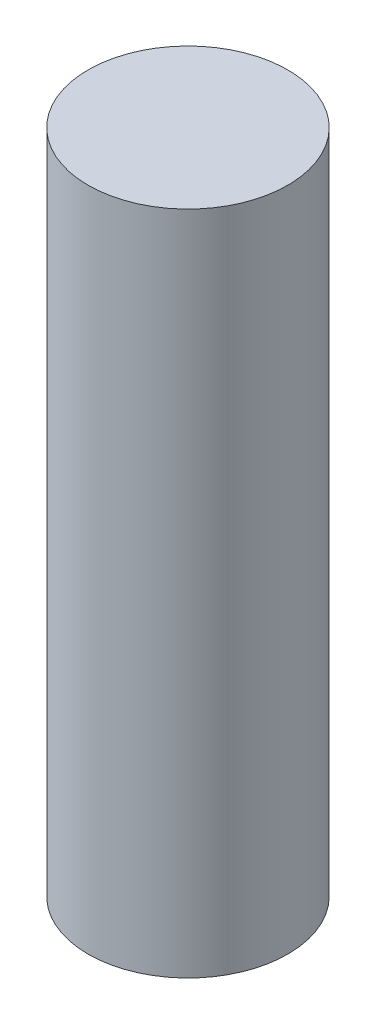
SolidWorks part; units mm, degrees
ref_plane "Front Plane" through (0, 0, 0) normal (0, 0, 1) x (1, 0, 0)
ref_plane "Top Plane" through (0, 0, 0) normal (0, 1, 0) x (1, 0, 0)
ref_plane "Right Plane" through (0, 0, 0) normal (1, 0, 0) x (0, 0, -1)
sketch "Sketch1" plane through (0, 0, 0) normal (0, 1, 0) x (1, 0, 0)
  circle A0 centre (0, 0) radius 0.75
  dimension "D1" = 1.5
extrude "Boss-Extrude1" add sketch "Sketch1" along normal blind 5
